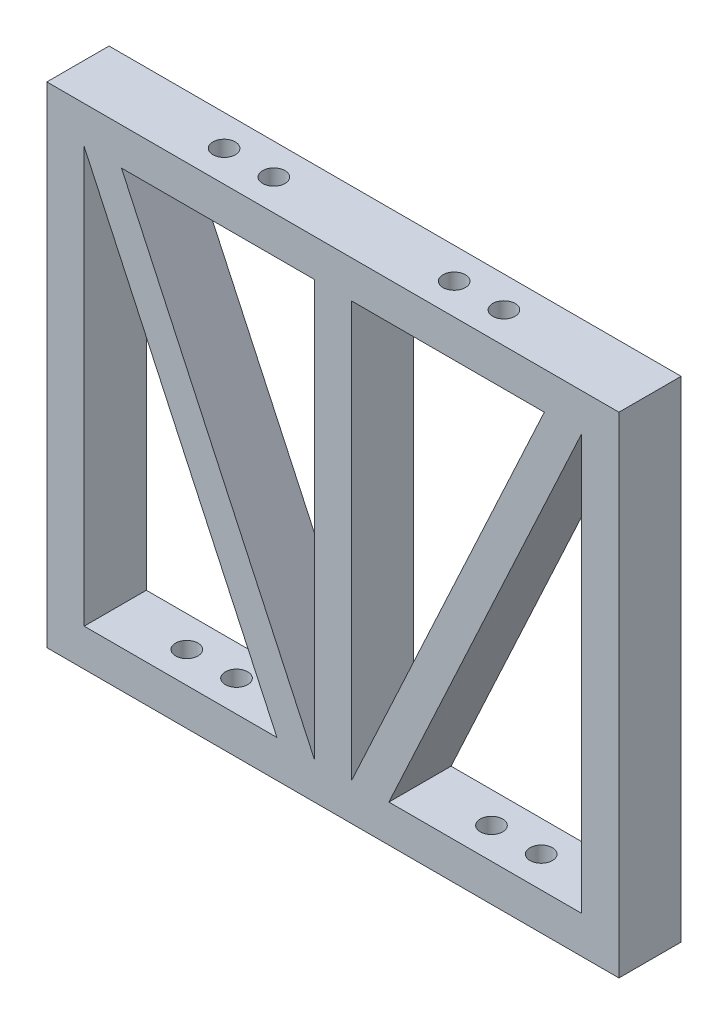
SolidWorks part; units mm, degrees
ref_plane "Front Plane" through (0, 0, 0) normal (0, 0, 1) x (1, 0, 0)
ref_plane "Top Plane" through (0, 0, 0) normal (0, 1, 0) x (1, 0, 0)
ref_plane "Right Plane" through (0, 0, 0) normal (1, 0, 0) x (0, 0, -1)
sketch "Sketch1" plane through (0, 0, 0) normal (0, 0, 1) x (1, 0, 0)
  line L1 (-29.21, 0) -> (29.21, 0)
  line L2 (-29.21, 0) -> (-29.21, 50.038)
  line L3 (-29.21, 50.038) -> (29.21, 50.038)
  line L4 (29.21, 0) -> (29.21, 50.038)
  line L28 (-25.4, 46.228) -> (-25.4, 3.81)
  line L29 (-25.4, 3.81) -> (-5.715, 3.81)
  line L30 (-5.715, 3.81) -> (-25.4, 46.228)
  line L31 (1.905, 46.228) -> (1.905, 3.81)
  line L32 (-21.59, 46.228) -> (-1.905, 3.81)
  line L33 (-1.905, 3.81) -> (-1.905, 46.228)
  line L34 (-1.905, 46.228) -> (-21.59, 46.228)
  line L35 (1.905, 3.81) -> (21.59, 46.228)
  line L36 (21.59, 46.228) -> (1.905, 46.228)
  line L37 (5.715, 3.81) -> (25.4, 46.228)
  line L38 (25.4, 46.228) -> (25.4, 3.81)
  line L39 (25.4, 3.81) -> (5.715, 3.81)
  dimension "D1" = 50.038
  dimension "D2" = 58.42
  dimension "D3" = 3.81
  dimension "D4" = 3.81
  dimension "D5" = 3.81
  dimension "D6" = 3.81
  dimension "D8" = 19.685
  dimension "D7" = 3.81
  dimension "D9" = 3.81
  dimension "D10" = 19.685
  dimension "D11" = 3.81
  dimension "D12" = 3.81
  dimension "D13" = 3.81
  dimension "D14" = 19.685
extrude "Boss-Extrude1" add sketch "Sketch1" along normal blind 6.35
sketch "Sketch2" plane through (0, 0, 0) normal (0, 1, 0) x (1, 0, 0)
  line L1 (-29.21, -6.35) -> (-29.21, 0) construction
  line L3 (29.21, 0) -> (-29.21, 0) construction
  line L4 (29.21, -6.35) -> (29.21, 0) construction
  circle A0 centre (-18.0975, -3.175) radius 1.143
  circle A1 centre (-13.0175, -3.175) radius 1.143
  circle A2 centre (18.0975, -3.175) radius 1.143
  circle A3 centre (13.0175, -3.175) radius 1.143
  point P10 (16.8269, 5.0289)
  point P17 (0, 0)
  point P18 (0, 0)
  point P19 (0, 0)
  dimension "D1" = 2.286
  dimension "D2" = 2.286
  dimension "D3" = 2.286
  dimension "D4" = 2.286
  dimension "D5" = 5.08
  dimension "D6" = 11.1125
  dimension "D7" = 5.08
  dimension "D8" = 11.1125
  dimension "D10" = 3.175
  dimension "D11" = 3.175
  dimension "D12" = 3.175
extrude "Cut-Extrude1" cut sketch "Sketch2" along normal blind 3.81
sketch "Sketch3" plane through (0, 50.038, 0) normal (0, 1, 0) x (1, 0, 0)
  line L0 (29.21, -6.35) -> (-29.21, -6.35) construction
  line L1 (-29.21, -6.35) -> (-29.21, 0) construction
  line L2 (29.21, -6.35) -> (29.21, 0) construction
  circle A0 centre (-14.2875, -3.175) radius 1.143
  circle A1 centre (-9.2075, -3.175) radius 1.143
  circle A2 centre (9.2075, -3.175) radius 1.143
  circle A3 centre (14.2875, -3.175) radius 1.143
  dimension "D1" = 2.286
  dimension "D2" = 2.286
  dimension "D3" = 2.286
  dimension "D4" = 2.286
  dimension "D12" = 14.9225
  dimension "D5" = 5.08
  dimension "D6" = 5.08
  dimension "D7" = 3.175
  dimension "D8" = 3.175
  dimension "D9" = 3.175
  dimension "D10" = 3.175
  dimension "D11" = 14.9225
extrude "Cut-Extrude2" cut sketch "Sketch3" against normal blind 3.81
